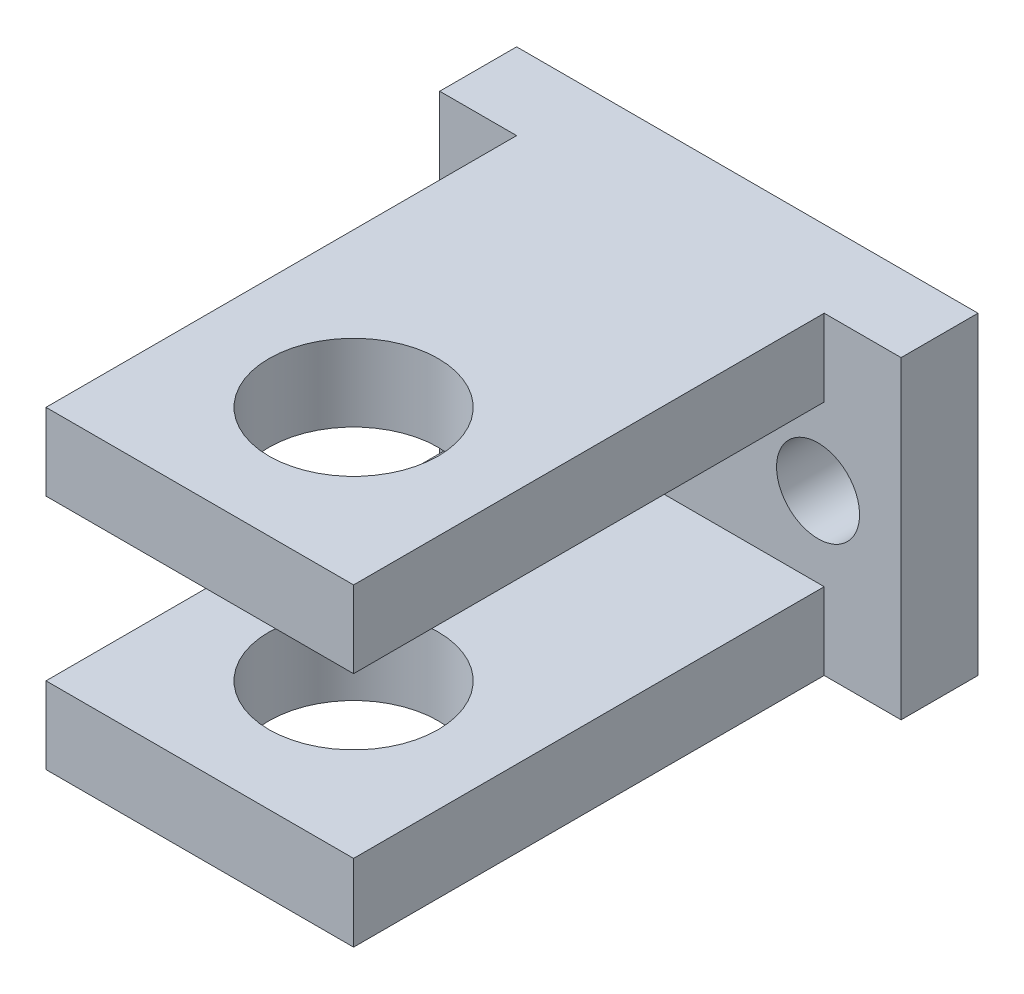
SolidWorks part; units mm, degrees
ref_plane "Front Plane" through (0, 0, 0) normal (0, 0, 1) x (1, 0, 0)
ref_plane "Top Plane" through (0, 0, 0) normal (0, 1, 0) x (1, 0, 0)
ref_plane "Right Plane" through (0, 0, 0) normal (1, 0, 0) x (0, 0, -1)
sketch "Sketch1" plane through (0, 0, 0) normal (0, 1, 0) x (1, 0, 0)
  line L1 (-6.35, -11.303) -> (6.35, -11.303)
  line L2 (-6.35, -11.303) -> (-6.35, 11.303)
  line L3 (-6.35, 11.303) -> (6.35, 11.303)
  line L4 (6.35, -11.303) -> (6.35, 11.303)
  line L5 (-6.35, -11.303) -> (6.35, 11.303) construction
  line L6 (-6.35, 11.303) -> (6.35, -11.303) construction
  point P0 (0, 0)
  dimension "D1" = 22.606
  dimension "D2" = 12.7
extrude "Boss-Extrude1" add sketch "Sketch1" along normal blind 3.175
sketch "Sketch2" plane through (0, 3.175, 0) normal (0, 1, 0) x (1, 0, 0)
  line L6 (-6.35, 11.303) -> (6.35, 11.303)
  line L7 (-6.35, 11.303) -> (-6.35, 8.128)
  line L8 (-6.35, 8.128) -> (6.35, 8.128)
  line L9 (6.35, 11.303) -> (6.35, 8.128)
  dimension "D2" = 3.175
extrude "Boss-Extrude2" add sketch "Sketch2" along normal blind 6.604
sketch "Sketch3" plane through (0, 9.779, 0) normal (0, 1, 0) x (1, 0, 0)
  line L1 (-6.35, 11.303) -> (6.35, 11.303)
  line L2 (-6.35, 11.303) -> (-6.35, -11.303)
  line L3 (-6.35, -11.303) -> (6.35, -11.303)
  line L4 (6.35, 11.303) -> (6.35, -11.303)
extrude "Boss-Extrude3" add sketch "Sketch3" along normal blind 3.175
sketch "Sketch4" plane through (0, 12.954, 0) normal (0, 1, 0) x (1, 0, 0)
  line L1 (-6.35, -11.303) -> (6.35, -11.303) construction
  circle A0 centre (0, -4.953) radius 3.4925
  dimension "D1" = 6.985
  dimension "D2" = 6.35
extrude "Cut-Extrude1" cut sketch "Sketch4" against normal through all
sketch "Sketch6" plane through (0, 0, -11.303) normal (0, 0, -1) x (-1, 0, 0)
  line L0 (-6.35, 12.954) -> (-9.525, 12.954)
  line L1 (-9.525, 12.954) -> (-9.525, 0)
  line L2 (-9.525, 0) -> (-6.35, 0)
  line L3 (-6.35, 0) -> (-6.35, 12.954)
  line L4 (6.35, 12.954) -> (9.525, 12.954)
  line L5 (9.525, 12.954) -> (9.525, 0)
  line L6 (9.525, 0) -> (6.35, 0)
  line L7 (6.35, 12.954) -> (6.35, 0) construction
  line L8 (6.35, 0) -> (6.35, 12.954)
  dimension "D1" = 3.175
  dimension "D2" = 3.175
extrude "Boss-Extrude4" add sketch "Sketch6" against normal blind 3.175
sketch "Sketch5" plane through (0, 0, -11.303) normal (0, 0, -1) x (-1, 0, 0)
  line L0 (0, 12.954) -> (0, 0) construction
  line L1 (-9.525, 12.954) -> (9.525, 12.954) construction
  line L2 (-6.35, 6.477) -> (6.35, 6.477) construction
  line L3 (-6.35, 12.954) -> (-6.35, 0) construction
  line L4 (6.35, 12.954) -> (6.35, 0) construction
  line L5 (9.525, 0) -> (9.525, 12.954) construction
  line L6 (-9.525, 12.954) -> (-9.525, 0) construction
  circle A0 centre (6.096, 6.477) radius 1.7145
  circle A1 centre (-6.096, 6.477) radius 1.7145
  point P15 (9.525, 6.477)
  dimension "D1" = 3.429
  dimension "D2" = 3.429
  dimension "D5" = 12.192
  dimension "D6" = 12.192
  dimension "D3" = 3.429
  dimension "D4" = 3.429
extrude "cut for mount screws" cut sketch "Sketch5" against normal through all
